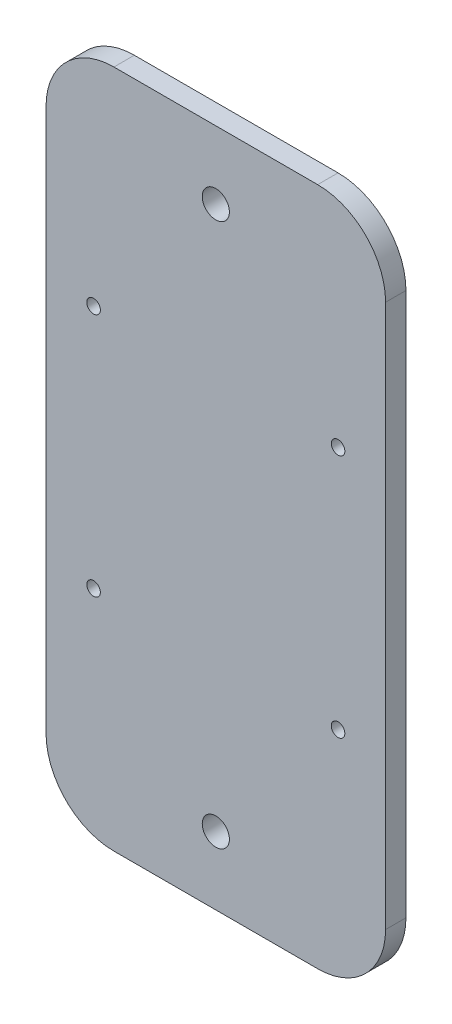
SolidWorks part; units mm, degrees
material "Pin"
ref_plane "Plan de face" through (0, 0, 0) normal (0, 0, 1) x (1, 0, 0)
ref_plane "Plan de dessus" through (0, 0, 0) normal (0, 1, 0) x (1, 0, 0)
ref_plane "Plan de droite" through (0, 0, 0) normal (1, 0, 0) x (0, 0, -1)
sketch "Esquisse1" plane through (0, 0, 0) normal (0, 0, 1) x (1, 0, 0)
  line L1 (-180.6338, 158.5299) -> (-80.6338, 158.5299)
  line L2 (-180.6338, 158.5299) -> (-180.6338, -41.4701)
  line L3 (-180.6338, -41.4701) -> (-80.6338, -41.4701)
  line L4 (-80.6338, 158.5299) -> (-80.6338, -41.4701)
  dimension "D1" = 100
  dimension "D2" = 200
extrude "Boss.-Extru.1" add sketch "Esquisse1" along normal blind 6
sketch "Esquisse2" plane through (0, 0, 6) normal (0, 0, 1) x (1, 0, 0)
  line L0 (-130.6338, 158.5299) -> (-130.6338, -41.4701) construction
  line L1 (-80.6338, 158.5299) -> (-180.6338, 158.5299) construction
  line L2 (-130.6338, 58.5299) -> (-130.6338, 94.5299) construction
  line L3 (-180.6338, 158.5299) -> (-180.6338, -41.4701) construction
  line L4 (-130.6338, 94.5299) -> (-166.6338, 94.5299) construction
  line L5 (-180.6338, -41.4701) -> (-80.6338, -41.4701) construction
  line L6 (-180.6338, 58.5299) -> (-80.6338, 58.5299) construction
  line L7 (-80.6338, -41.4701) -> (-80.6338, 158.5299) construction
  line L8 (-166.6338, 94.5299) -> (-166.6338, 58.5299) construction
  circle A5 centre (-166.6338, 94.5299) radius 2
  circle A6 centre (-166.6338, 22.5299) radius 2
  circle A7 centre (-94.6338, 22.5299) radius 2
  circle A8 centre (-94.6338, 94.5299) radius 2
  circle A9 centre (-130.6338, 138.5299) radius 4
  circle A10 centre (-130.6338, -21.4701) radius 4
  point P27 (-130.6338, 73.5299)
  dimension "D1" = 4
  dimension "D2" = 8
  dimension "D3" = 20
extrude "Enlèv. mat.-Extru.1" cut sketch "Esquisse2" against normal up to surface (6 mm away) up to face at (-130.6338, 58.5299, 0)
fillet "Congé1" radius 20 4 edges at (-180.6338, -41.4701, 3) (-80.6338, -41.4701, 3) (-80.6338, 158.5299, 3) (-180.6338, 158.5299, 3)
